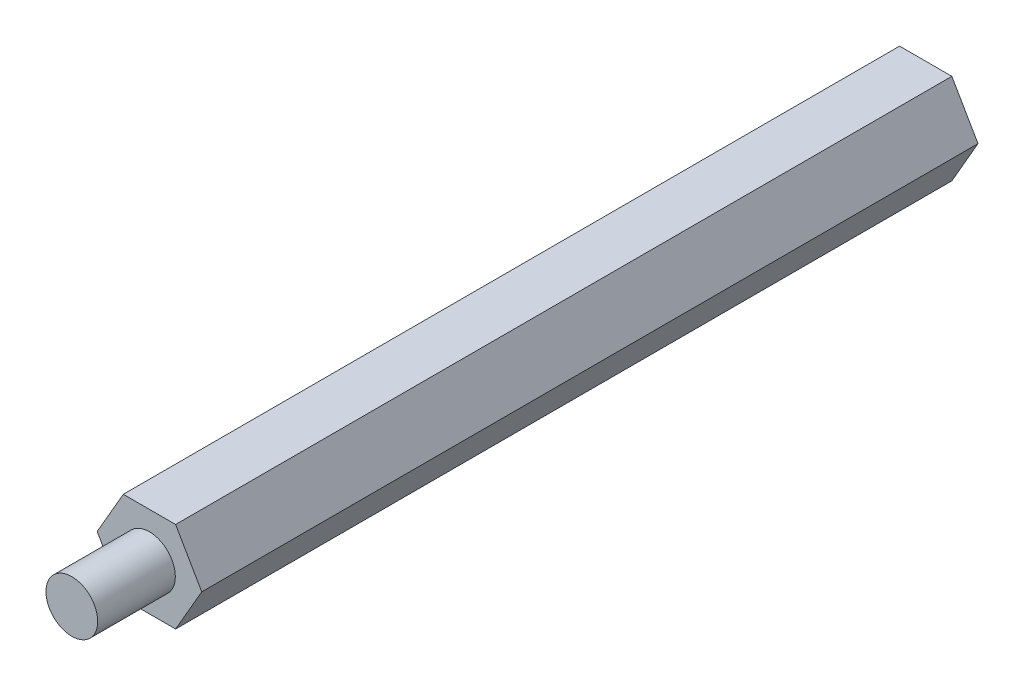
SolidWorks part; units mm, degrees
material "黃銅"
ref_plane "前基準面" through (0, 0, 0) normal (0, 0, 1) x (1, 0, 0)
ref_plane "上基準面" through (0, 0, 0) normal (0, 1, 0) x (1, 0, 0)
ref_plane "右基準面" through (0, 0, 0) normal (1, 0, 0) x (0, 0, -1)
sketch "草圖1" plane through (0, 0, 0) normal (0, 0, 1) x (1, 0, 0)
  line L1 (4.0415, 0) -> (2.0207, 3.5)
  line L2 (2.0207, 3.5) -> (-2.0207, 3.5)
  line L3 (-2.0207, 3.5) -> (-4.0415, 0)
  line L4 (-4.0415, 0) -> (-2.0207, -3.5)
  line L5 (-2.0207, -3.5) -> (2.0207, -3.5)
  line L6 (2.0207, -3.5) -> (4.0415, 0)
  circle A0 centre (0, 0) radius 3.5 construction
  dimension "D1" = 7
extrude "填料-伸長1" add sketch "草圖1" along normal blind 60
sketch "草圖2" plane through (0, 0, 60) normal (0, 0, 1) x (1, 0, 0)
  circle A0 centre (0, 0) radius 2
  dimension "D1" = 4
extrude "填料-伸長2" add sketch "草圖2" along normal blind 6
hole_wizard "M4x0.7 螺紋孔1" positions "草圖4" profile "草圖5" tap size "M4x0.7" standard "Ansi Metric"
sketch "草圖4" plane through (0, 0, 0) normal (0, 0, -1) x (-1, 0, 0)
  point P0 (0, 0)
sketch "草圖5" plane through (0, 0, 0) normal (1, 0, 0) x (0, 1, 0)
  line L0 (0, 0) -> (0, 11.4914)
  line L1 (0, 11.4914) -> (1.65, 10.5)
  line L2 (1.65, 10.5) -> (1.65, 0)
  line L5 (1.65, 0) -> (0, 0)
  line L10 (0, 11.4914) -> (-1.65, 10.5) construction
  line L11 (0, -6.35) -> (0, 107.95) construction
  dimension "螺孔鑽直徑" = 3.3
  dimension "螺孔鑽深度" = 10.5
  dimension "導頭角度" = 118
cosmetic thread "鑽孔螺紋1" parameters "D1"=8, "D2"=4
